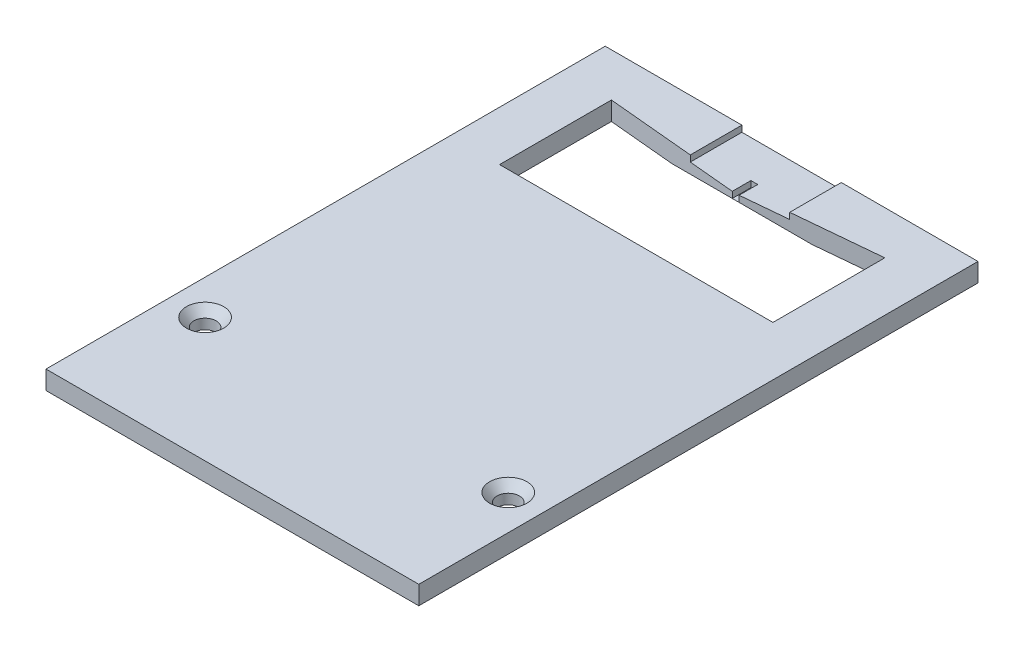
SolidWorks part; units mm, degrees
ref_plane "Front Plane" through (0, 0, 0) normal (0, 0, 1) x (1, 0, 0)
ref_plane "Top Plane" through (0, 0, 0) normal (0, 1, 0) x (1, 0, 0)
ref_plane "Right Plane" through (0, 0, 0) normal (1, 0, 0) x (0, 0, -1)
sketch "Sketch1" plane through (0, 0, 0) normal (0, 1, 0) x (1, 0, 0)
  line L0 (-22, 45) -> (22, 45)
  line L1 (-22, 61) -> (-22, 45)
  line L2 (-30, 20) -> (-30, -20)
  line L3 (-30, -20) -> (30, -20)
  line L4 (30, 20) -> (30, -20)
  line L5 (-22, 70) -> (22, 70)
  line L6 (-30, 20) -> (-30, 70)
  line L7 (-30, 70) -> (-22, 70)
  line L8 (22, 61) -> (22, 45)
  line L9 (30, 20) -> (30, 70)
  line L10 (30, 70) -> (22, 70)
  line L13 (-22, 61) -> (22, 61)
extrude "Boss-Extrude1" add sketch "Sketch1" along normal blind 3
sketch "Sketch3" plane through (0, 3, 0) normal (0, 1, 0) x (1, 0, 0)
  line L0 (22, 61) -> (-22, 61) construction
  line L1 (-8, 61) -> (8, 61)
  line L2 (-8, 61) -> (-8, 70)
  line L3 (-8, 70) -> (8, 70)
  line L4 (8, 61) -> (8, 70)
  line L5 (30, 70) -> (-30, 70) construction
extrude "Cut-Extrude2" cut sketch "Sketch3" against normal blind 1
sketch "Sketch4" plane through (0, 2, 0) normal (0, 1, 0) x (1, 0, 0)
  line L0 (-8, 61) -> (8, 61) construction
  line L1 (-0.55, 64) -> (0.55, 64)
  line L2 (-0.55, 64) -> (-0.55, 61)
  line L3 (-0.55, 61) -> (0.55, 61)
  line L4 (0.55, 64) -> (0.55, 61)
extrude "Cut-Extrude3" cut sketch "Sketch4" against normal blind 1
sketch "Sketch5" plane through (0, 3, 0) normal (0, 1, 0) x (1, 0, 0)
  circle A0 centre (24.4, 0) radius 3
  circle A1 centre (-24.4, 0) radius 3
extrude "Cut-Extrude4" cut sketch "Sketch5" against normal through all draft 41
sketch "Sketch7" plane through (0, 3, 0) normal (0, 1, 0) x (1, 0, 0)
  circle A0 centre (-24.4, 0) radius 1.8
  circle A1 centre (24.4, 0) radius 1.8
extrude "Cut-Extrude5" cut sketch "Sketch7" against normal through all
sketch "Sketch8" plane through (0, 3, 0) normal (0, 1, 0) x (1, 0, 0)
  line L0 (-22, 61) -> (-0.55, 61)
  line L1 (-0.55, 61) -> (-22, 63)
  line L2 (-22, 63) -> (-22, 61)
  line L3 (22, 61) -> (0.55, 61)
  line L4 (0.55, 61) -> (22, 63)
  line L5 (22, 63) -> (22, 61)
extrude "Cut-Extrude7" cut sketch "Sketch8" against normal through all
sketch "Sketch9" plane through (0, 0, 0) normal (0, -1, 0) x (1, 0, 0)
  line L0 (22, -45) -> (22, -63) construction
  line L1 (22, -62) -> (-22, -62)
  line L2 (22, -62) -> (22, -60)
  line L3 (22, -60) -> (-22, -60)
  line L4 (-22, -62) -> (-22, -60)
  line L5 (-22, -63) -> (-22, -45) construction
extrude "Cut-Extrude8" cut sketch "Sketch9" against normal blind 1 draft 45
